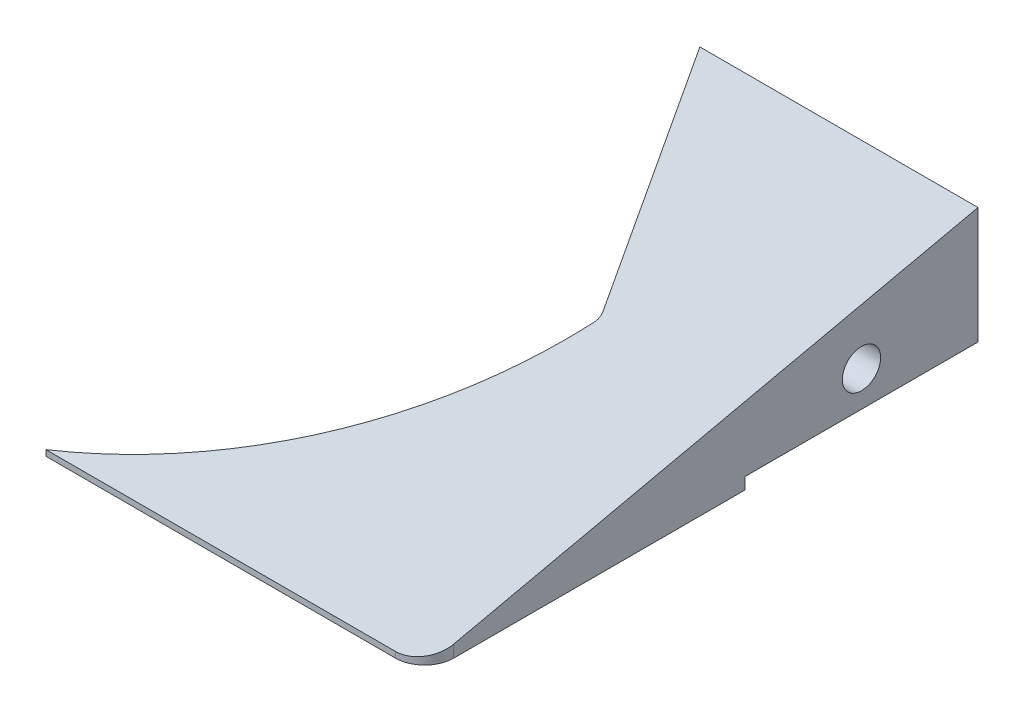
SolidWorks part; units mm, degrees
material "AISI 4340 Aço, normalizado"
ref_plane "Plano frontal" through (0, 0, 0) normal (0, 0, 1) x (1, 0, 0)
ref_plane "Plano superior" through (0, 0, 0) normal (0, 1, 0) x (1, 0, 0)
ref_plane "Plano direito" through (0, 0, 0) normal (1, 0, 0) x (0, 0, -1)
sketch "Esboço1" plane through (0, 0, 0) normal (0, 0, 1) x (1, 0, 0)
  line L1 (-65, 11) -> (65, 11)
  line L2 (-65, 11) -> (-65, -11)
  line L3 (-65, -11) -> (65, -11)
  line L4 (65, 11) -> (65, -11)
  line L5 (-65, 11) -> (65, -11) construction
  line L6 (-65, -11) -> (65, 11) construction
  point P0 (0, 0)
  dimension "D1" = 130
  dimension "D2" = 22
extrude "Ressalto-extrusão1" add sketch "Esboço1" along normal blind 95
sketch "Esboço2" plane through (0, 11, 0) normal (0, 1, 0) x (1, 0, 0)
  line L0 (17.25, 0) -> (-65, 0)
  line L2 (65, -95) -> (65, 0) construction
  line L3 (40.2, -40) -> (17.25, 0)
  line L4 (-65, -95) -> (-65, 0) construction
  line L6 (-65, -95) -> (-65, 0)
  line L7 (65, -95) -> (-65, -95) construction
  line L8 (65, 0) -> (-65, 0) construction
  line L9 (0, -95) -> (-65, -95)
  arc A0 (0, -95) -> (40.2, -40) centre (-32.455, -29.0871) ccw
  dimension "D3" = 65
  dimension "D5" = 73.47
  dimension "D1" = 47.75
  dimension "D2" = 24.8
  dimension "D4" = 40
extrude "Corte-extrusão2" cut sketch "Esboço2" against normal up to next contours A0 L3 L0 L6 L9
sketch "Esboço3" plane through (65, 0, 0) normal (1, 0, 0) x (0, 0, -1)
  line L0 (0, 11) -> (-95, -10)
  line L1 (-95, -11) -> (-95, 11) construction
  dimension "D1" = 1
extrude "Corte-extrusão3" cut sketch "Esboço3" against normal through all and the other way through all flip side to cut
hole_wizard "Broca de rosquear de cano para tarraxa de 1/82" positions "Esboço7" profile "Esboço8" hole size "1/8" standard "Ansi Inch"
sketch "Esboço7" plane through (65, 0, 0) normal (1, 0, 0) x (0, 0, -1)
  line L0 (0, -11) -> (0, 11) construction
  line L1 (-95, -11) -> (0, -11) construction
  point P0 (-20, -2.945)
  dimension "D1" = 20
  dimension "D2" = 8.055
sketch "Esboço8" plane through (65, -2.945, 20) normal (0, 1, 0) x (0, 0, -1)
  line L0 (0, 0) -> (0, 11.9768)
  line L1 (0, 11.9768) -> (3.29, 10)
  line L2 (3.29, 10) -> (3.29, 0)
  line L5 (3.29, 0) -> (0, 0)
  line L10 (0, 11.9768) -> (-3.29, 10) construction
  line L11 (0, -6.35) -> (0, 107.95) construction
  dimension "Hole Dia." = 6.58
  dimension "Hole Depth" = 10
  dimension "Drill Angle" = 118
hole_wizard "Broca de rosquear de cano para tarraxa de 1/83" positions "Esboço10" profile "Esboço11" hole size "1/8" standard "Ansi Inch"
sketch "Esboço10" plane through (12.9778, 0, -7.446) normal (-0.8674, 0, 0.4977) x (0.4977, 0, 0.8674)
  line L0 (8.5846, -11) -> (8.5846, 11) construction
  line L1 (8.5846, -11) -> (54.7008, -11) construction
  point P0 (28.5846, -2.945)
  dimension "D1" = 20
  dimension "D2" = 8.055
sketch "Esboço11" plane through (27.2031, -2.945, 17.3475) normal (0, 1, 0) x (0.4977, 0, 0.8674)
  line L0 (0, 0) -> (0, 11.9768)
  line L1 (0, 11.9768) -> (3.29, 10)
  line L2 (3.29, 10) -> (3.29, 0)
  line L5 (3.29, 0) -> (0, 0)
  line L10 (0, 11.9768) -> (-3.29, 10) construction
  line L11 (0, -6.35) -> (0, 107.95) construction
  dimension "Hole Dia." = 6.58
  dimension "Hole Depth" = 10
  dimension "Drill Angle" = 118
fillet "Filete2" radius 5 1 edges at (65, -10.5, 95)
sketch "Esboço16" plane through (0, 0, 0) normal (0, 0, -1) x (-1, 0, 0)
  line L0 (-65, -11) -> (-17.25, -11)
  line L1 (-17.25, -11) -> (-17.25, -9)
  line L2 (-17.25, -11) -> (-17.25, 11) construction
  line L3 (-17.25, -9) -> (-65, -9)
  line L4 (-65, -9) -> (-65, -11)
  dimension "D1" = 2
extrude "Corte-extrusão6" cut sketch "Esboço16" against normal blind 40
fillet "Filete3" radius 3 1 edges at (40.2, -3.4211, 40)
